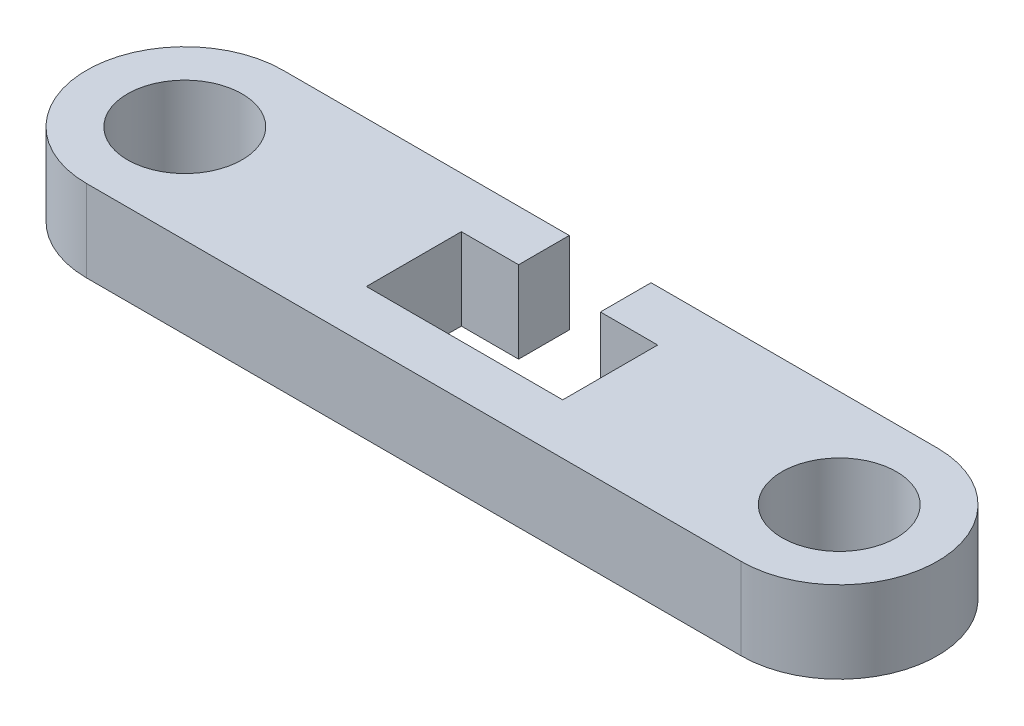
SolidWorks part; units mm, degrees
ref_plane "Front Plane" through (0, 0, 0) normal (0, 0, 1) x (1, 0, 0)
ref_plane "Top Plane" through (0, 0, 0) normal (0, 1, 0) x (1, 0, 0)
ref_plane "Right Plane" through (0, 0, 0) normal (1, 0, 0) x (0, 0, -1)
sketch "Sketch1" plane through (0, 0, 0) normal (0, 1, 0) x (1, 0, 0)
  line L0 (0, 0) -> (7, 0)
  line L1 (7, 0) -> (7, 4)
  line L2 (7, 4) -> (4.75, 4)
  line L3 (4.75, 4) -> (4.75, 3.4518)
  line L4 (4.75, 3.4518) -> (6.5, 3.4518)
  line L5 (6.5, 3.4518) -> (6.5, 0.55)
  line L6 (6.5, 0.55) -> (0.5, 0.55)
  line L7 (0.5, 0.55) -> (0.5, 3.4518)
  line L8 (0.5, 3.4518) -> (2.25, 3.4518)
  line L9 (2.25, 3.4518) -> (2.25, 4)
  line L10 (2.25, 4) -> (0, 4)
  line L11 (0, 4) -> (0, 0)
  line L12 (-6.5, 5) -> (2.25, 5)
  line L13 (-6.5, -1) -> (13.5, -1)
  line L14 (2.25, 5) -> (2.25, 4)
  line L15 (13.5, 5) -> (4.75, 5)
  line L16 (4.75, 5) -> (4.75, 4)
  line L17 (2.25, 5) -> (2.25, 4)
  circle A0 centre (-6.5, 2) radius 1.75
  circle A1 centre (13.5, 2) radius 1.75
  circle A2 centre (-6.5, 2) radius 3
  circle A3 centre (13.5, 2) radius 3
  dimension "D1" = 7
  dimension "D2" = 4
  dimension "D3" = 4
  dimension "D4" = 2.5
  dimension "D5" = 2.25
  dimension "D6" = 0.5482
  dimension "D7" = 0.55
  dimension "D8" = 6
  dimension "D9" = 0.5
extrude "Boss-Extrude1" add sketch "Sketch1" along normal blind 2.5 contours A2 A0 | A3 L15 L16 L2 L1 L0 L11 L10 L14 L12 A2 L13 | L10 L11 L0 L1 L2 L3 L4 L5 L6 L7 L8 L9 | A3 A1
